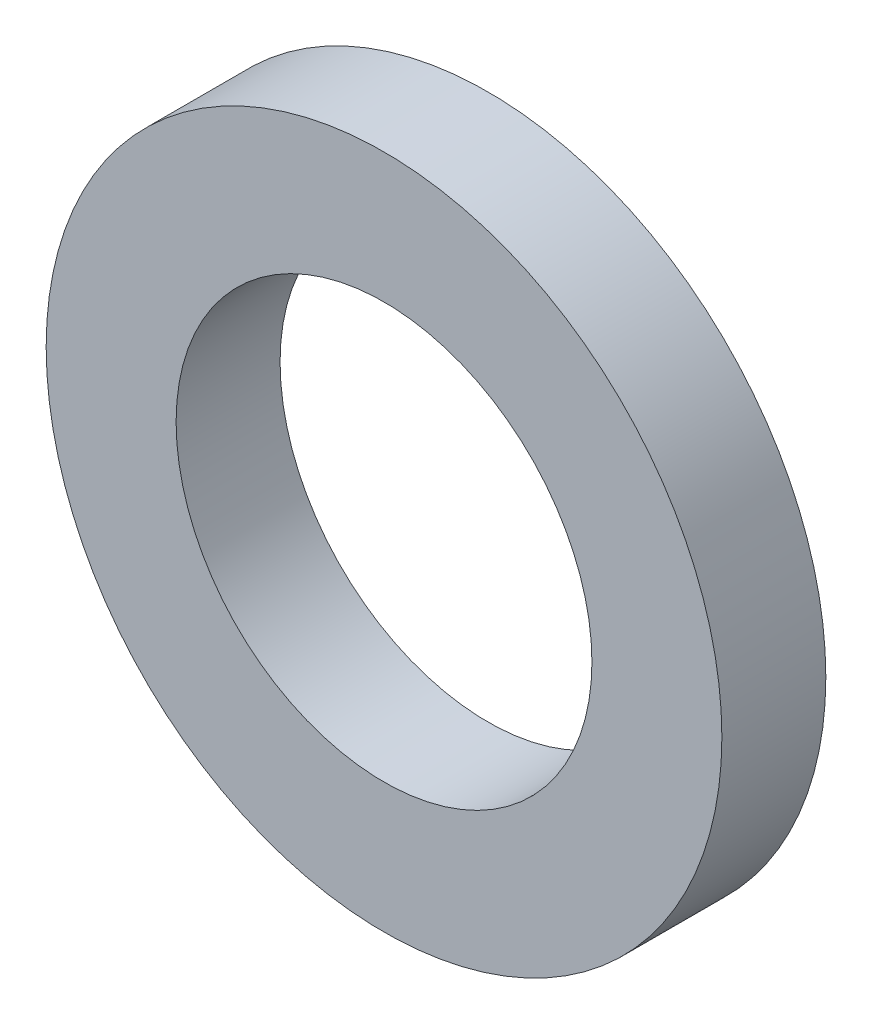
SolidWorks part; units mm, degrees
ref_plane "Front Plane" through (0, 0, 0) normal (0, 0, 1) x (1, 0, 0)
ref_plane "Top Plane" through (0, 0, 0) normal (0, 1, 0) x (1, 0, 0)
ref_plane "Right Plane" through (0, 0, 0) normal (1, 0, 0) x (0, 0, -1)
sketch "Sketch1" plane through (0, 0, 0) normal (0, 0, 1) x (1, 0, 0)
  circle A0 centre (0, 0) radius 4
  circle A1 centre (0, 0) radius 6.5
  dimension "D1" = 8
  dimension "D2" = 13
extrude "Boss-Extrude1" add sketch "Sketch1" along normal blind 2
